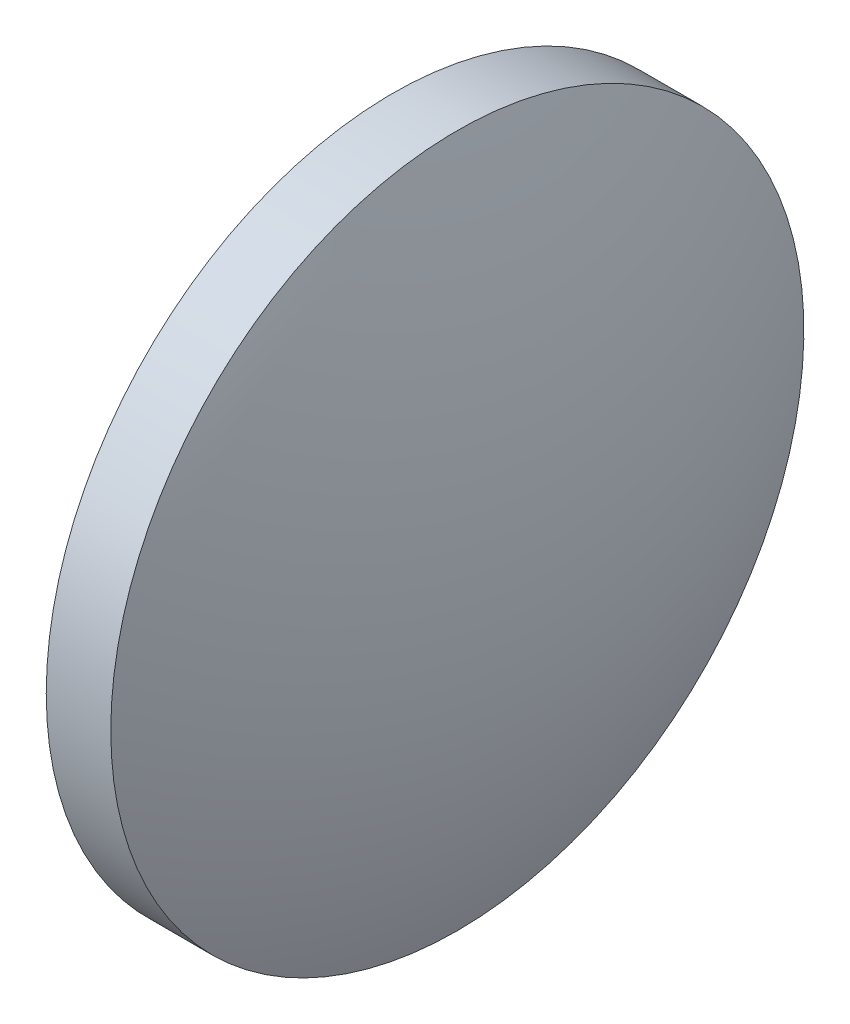
SolidWorks part; units mm, degrees
ref_plane "前视基准面" through (0, 0, 0) normal (0, 0, 1) x (1, 0, 0)
ref_plane "上视基准面" through (0, 0, 0) normal (0, 1, 0) x (1, 0, 0)
ref_plane "右视基准面" through (0, 0, 0) normal (1, 0, 0) x (0, 0, -1)
sketch "草图1" plane through (0, 0, 0) normal (0, 0, 1) x (1, 0, 0)
  line L0 (534.7244, 122.0834) -> (542.9917, 122.0834) construction
  line L1 (536.6472, 122.0834) -> (536.6472, 130.0834)
  line L2 (539.7472, 122.0834) -> (536.6472, 122.0834)
  line L5 (536.6472, 130.0834) -> (538.1372, 130.0834)
  arc A0 (539.7472, 122.0834) -> (538.1372, 130.0834) centre (519.0664, 122.0834) ccw
revolve "旋转1" add sketch "草图1" angle 360 about L0
